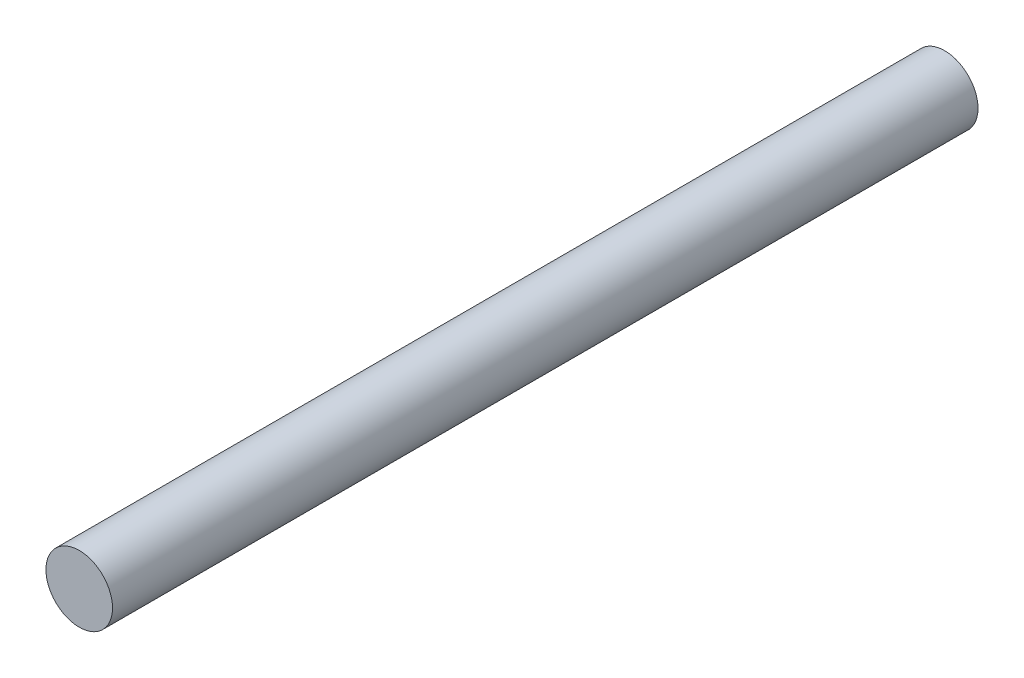
SolidWorks part; units mm, degrees
ref_plane "Front Plane" through (0, 0, 0) normal (0, 0, 1) x (1, 0, 0)
ref_plane "Top Plane" through (0, 0, 0) normal (0, 1, 0) x (1, 0, 0)
ref_plane "Right Plane" through (0, 0, 0) normal (1, 0, 0) x (0, 0, -1)
sketch "Sketch1" plane through (0, 0, 0) normal (0, 0, 1) x (1, 0, 0)
  circle A0 centre (0, 0) radius 5
extrude "Boss-Extrude1" add sketch "Sketch1" along normal blind 130
